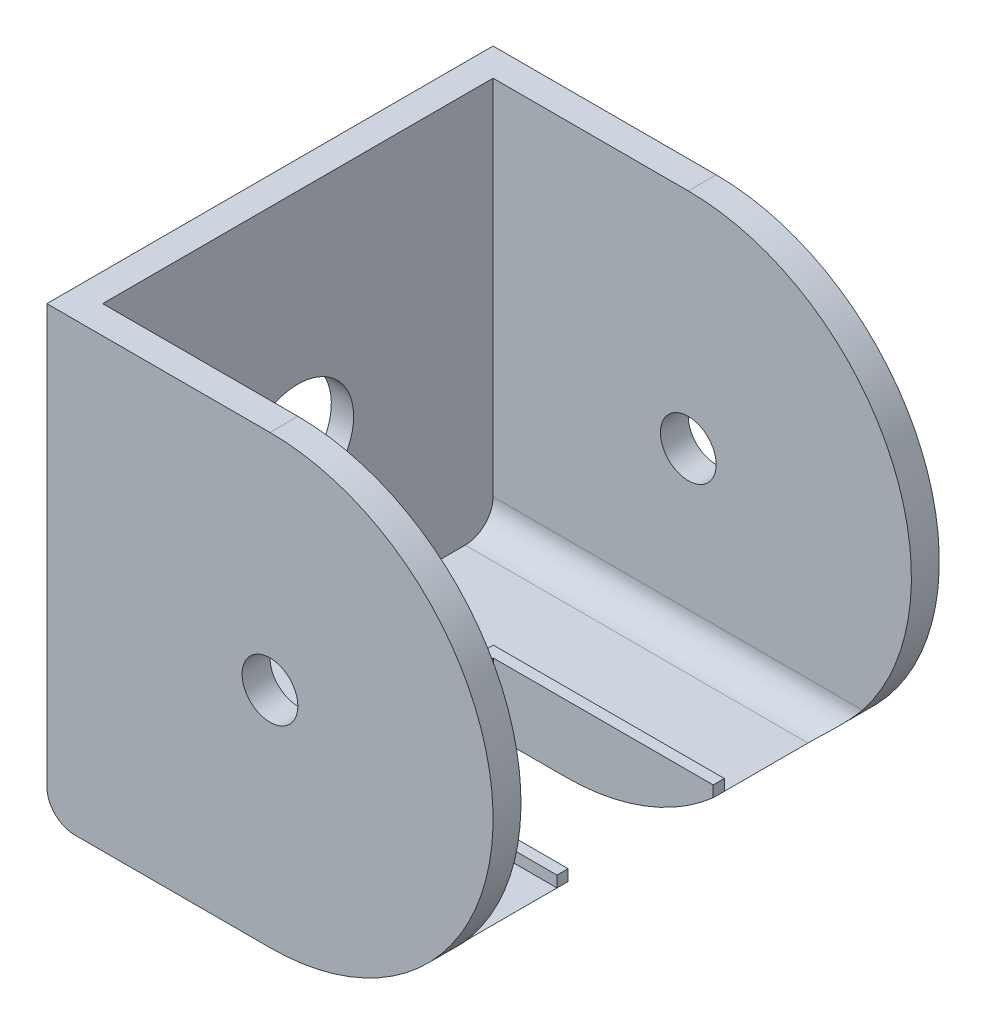
SolidWorks part; units mm, degrees
material "Custom Plastic"
ref_plane "Front Plane" through (0, 0, 0) normal (0, 0, 1) x (1, 0, 0)
ref_plane "Top Plane" through (0, 0, 0) normal (0, 1, 0) x (1, 0, 0)
ref_plane "Right Plane" through (0, 0, 0) normal (1, 0, 0) x (0, 0, -1)
sketch "Sketch1" plane through (0, 0, 0) normal (0, 0, 1) x (1, 0, 0)
  line L0 (72.2954, 0) -> (-7.7046, 0)
  line L1 (-7.7046, -40) -> (32.2954, -40)
  line L2 (-7.7046, -40) -> (-7.7046, 40)
  line L3 (-7.7046, 40) -> (32.2954, 40)
  line L5 (0, 0) -> (-7.7029, 0.3675) construction
  line L6 (0, 0) -> (-7.7029, -0.3675) construction
  arc A0 (-7.7029, 0.3675) -> (-7.7029, -0.3675) centre (32.2954, 0) ccw
  arc A1 (32.2954, -40) -> (32.2954, 40) centre (32.2954, 0) ccw
  circle A2 centre (32.2954, 0) radius 5
  point P0 (0, 0)
  dimension "D3" = 10
  dimension "D1" = 80
  dimension "D2" = 80
extrude "Boss-Extrude1" add sketch "Sketch1" along normal blind 5
sketch "Sketch2" plane through (0, 0, 5) normal (0, 0, 1) x (1, 0, 0)
  line L0 (-7.7046, 40) -> (-2.7046, 40)
  line L1 (-7.7046, 40) -> (32.2954, 40) construction
  line L2 (-2.7046, 40) -> (-2.7046, -40)
  line L3 (-7.7046, -40) -> (32.2954, -40) construction
  line L4 (-2.7046, -40) -> (-7.7046, -40)
  line L5 (-7.7046, -40) -> (-7.7046, 40)
  dimension "D1" = 5
extrude "Boss-Extrude2" add sketch "Sketch2" along normal blind 70
ref_plane "Plane1" through (0, 0, 40) normal (0, 0, 1) x (1, 0, 0)
mirror "Mirror1" about plane through (0, 0, 40) normal (0, 0, 1) of "Boss-Extrude1"
sketch "Sketch4" plane through (0, 0, 5) normal (0, 0, 1) x (1, 0, 0)
  line L0 (-2.7046, -40) -> (-2.7046, -30)
  line L1 (-2.7046, -40) -> (-2.7046, 40) construction
  line L2 (-2.7046, -30) -> (43.4973, -30)
  line L3 (43.4973, -30) -> (58.7529, -30)
  line L4 (-2.7046, -40) -> (32.2954, -40)
  arc A2 (32.2954, -40) -> (58.7529, -30) centre (32.2954, 0) ccw
  dimension "D1" = 10
extrude "Boss-Extrude3" add sketch "Sketch4" along normal blind 70
sketch "Sketch5" plane through (-7.7046, 0, 0) normal (-1, 0, 0) x (0, 0, 1)
  line L0 (0, 40) -> (80, -40)
  circle A0 centre (40, 0) radius 10
  dimension "D1" = 20
extrude "Cut-Extrude1" cut sketch "Sketch5" against normal blind 5 contours L0 A0 | L0 A0
sketch "Sketch6" plane through (-7.7046, 0, 0) normal (-1, 0, 0) x (0, 0, 1)
  circle A0 centre (40, 0) radius 20
  dimension "D1" = 40
extrude "Cut-Extrude2" cut sketch "Sketch6" against normal blind 1
sketch "Sketch7" plane through (0, -30, 0) normal (0, 1, 0) x (1, 0, 0)
  line L1 (-2.7046, -75) -> (-2.7046, -5) construction
  line L2 (58.7529, -75) -> (58.7529, -5) construction
  line L3 (58.7529, -40) -> (58.7529, -27)
  line L4 (58.7529, -27) -> (-2.7046, -27)
  line L5 (-2.7046, -27) -> (-2.7046, -40)
  line L6 (-2.7046, -40) -> (-2.7046, -53)
  line L7 (-2.7046, -53) -> (58.7529, -53)
  line L8 (58.7529, -53) -> (58.7529, -40)
  line L9 (19.3397, -53) -> (19.3397, -27)
  line M10 (58.7529, -75) -> (58.7529, -5)
  dimension "D1" = 13
  dimension "D2" = 13
extrude "Cut-Extrude3" cut sketch "Sketch7" against normal blind 19 contours L9 L7 L4 M10
sketch "Sketch8" plane through (0, -30, 0) normal (0, 1, 0) x (1, 0, 0)
  line L0 (58.7529, -53) -> (19.3397, -53)
  line L1 (19.3397, -53) -> (19.3397, -27)
  line L2 (19.3397, -27) -> (58.7529, -27)
  line L3 (58.7529, -27) -> (58.7529, -25)
  line L5 (58.7529, -55) -> (17.3397, -55)
  line L6 (17.3397, -55) -> (17.3397, -25)
  line L7 (17.3397, -25) -> (56.7529, -25)
  line L8 (58.7529, -55) -> (58.7529, -53)
  line L9 (56.7529, -25) -> (58.7529, -25)
  line L10 (58.7529, -27) -> (58.7529, -24.2721) construction
  line L11 (56.7529, -25) -> (56.7529, -24.2721) construction
  dimension "D1" = 2
extrude "Boss-Extrude4" add sketch "Sketch8" along normal blind 2
fillet "Fillet1" radius 5 3 edges at (-7.7046, -40, 40) (28.0241, -30, 5) (28.0241, -30, 75)
